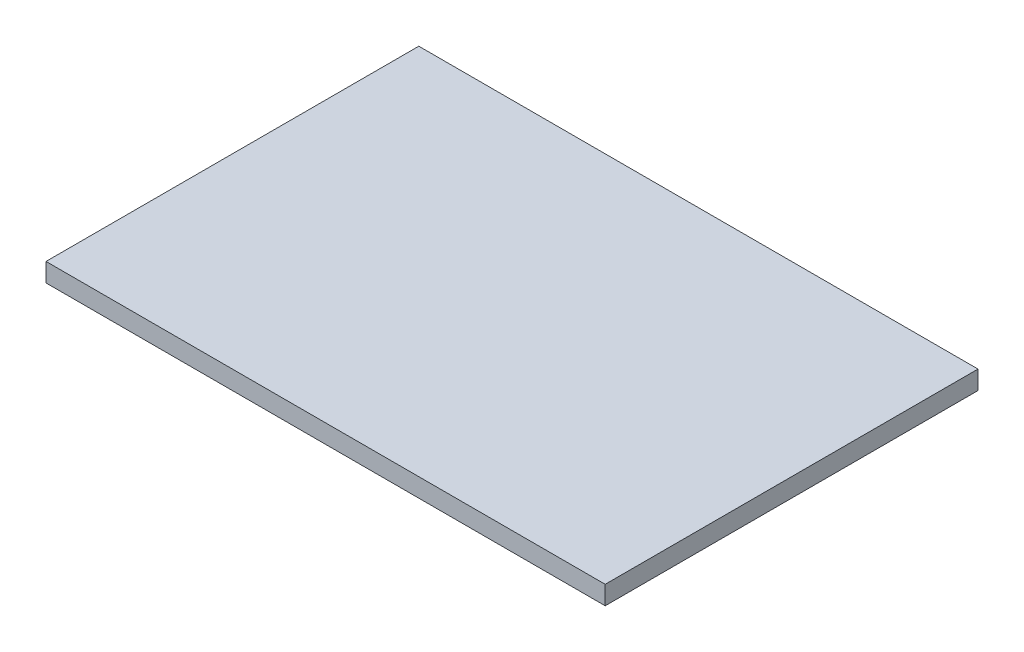
SolidWorks part; units mm, degrees
ref_plane "Front Plane" through (0, 0, 0) normal (0, 0, 1) x (1, 0, 0)
ref_plane "Top Plane" through (0, 0, 0) normal (0, 1, 0) x (1, 0, 0)
ref_plane "Right Plane" through (0, 0, 0) normal (1, 0, 0) x (0, 0, -1)
sketch "Sketch2" plane through (0, 0, 0) normal (1, 0, 0) x (0, 0, -1)
  line L0 (0, 0) -> (-100, 0)
  line L1 (-100, 0) -> (-100, 5)
  line L2 (-100, 5) -> (0, 5)
  line L3 (0, 5) -> (0, 0)
extrude "Boss-Extrude1" add sketch "Sketch2" against normal blind 150
